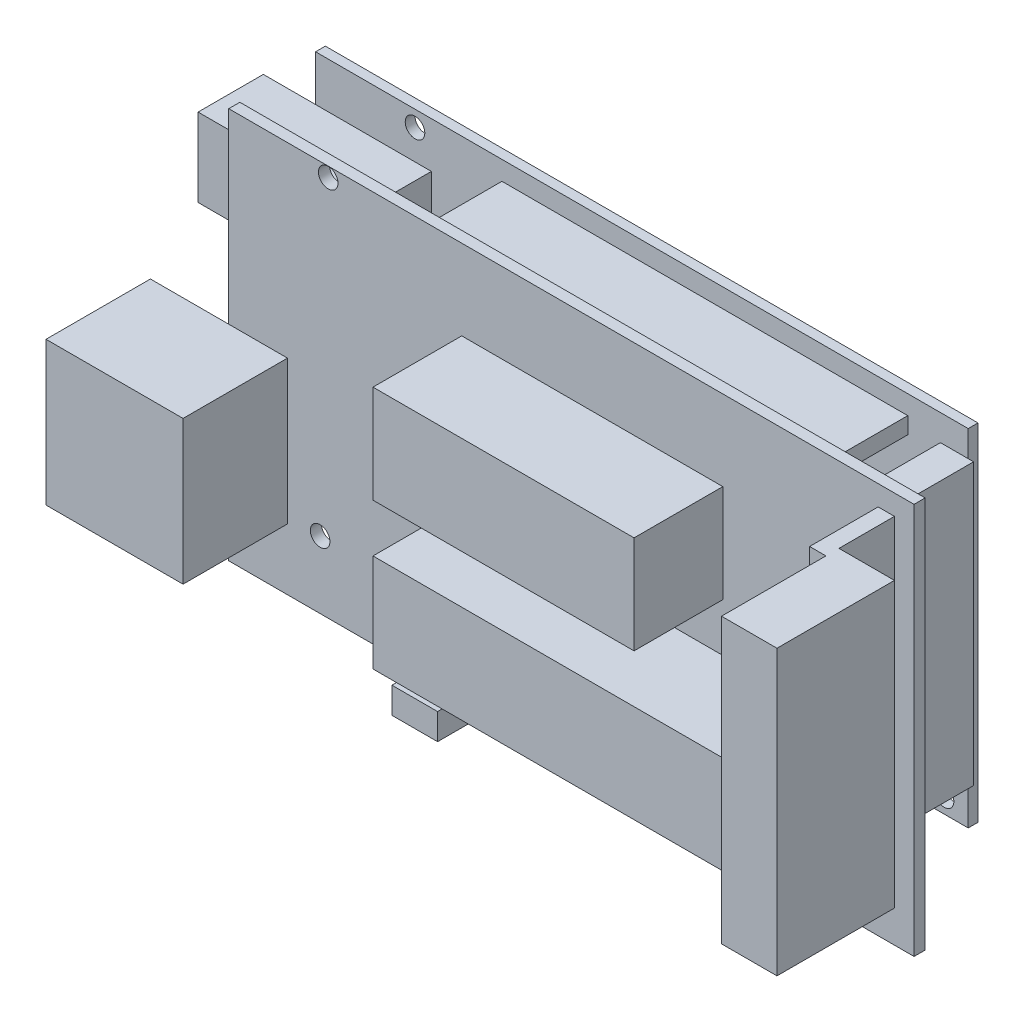
SolidWorks part; units mm, degrees
ref_plane "Plano frontal" through (0, 0, 0) normal (0, 0, 1) x (1, 0, 0)
ref_plane "Plano superior" through (0, 0, 0) normal (0, 1, 0) x (1, 0, 0)
ref_plane "Plano direito" through (0, 0, 0) normal (1, 0, 0) x (0, 0, -1)
sketch "Esboço1" plane through (0, 0, 0) normal (0, 0, 1) x (1, 0, 0)
  line L1 (-52.5, 30) -> (52.5, 30)
  line L2 (-52.5, 30) -> (-52.5, -30)
  line L3 (-52.5, -30) -> (52.5, -30)
  line L4 (52.5, 30) -> (52.5, -30)
  line L5 (-52.5, 30) -> (52.5, -30) construction
  line L6 (-52.5, -30) -> (52.5, 30) construction
  point P0 (0, 0)
  dimension "D1" = 60
  dimension "D2" = 105
extrude "Ressalto-extrusão1" add sketch "Esboço1" along normal blind 1.7
sketch "Esboço2" plane through (0, 0, 1.7) normal (0, 0, 1) x (1, 0, 0)
  line L0 (-52.5, -30) -> (52.5, -30) construction
  line L1 (-16.8, -4.7) -> (43.2, -4.7)
  line L2 (-16.8, -4.7) -> (-16.8, -19.7)
  line L3 (-16.8, -19.7) -> (43.2, -19.7)
  line L4 (43.2, -4.7) -> (43.2, -19.7)
  line L5 (52.5, -30) -> (52.5, 30) construction
  line L7 (-16.8, 2.7) -> (23.2, 2.7)
  line L8 (-16.8, 2.7) -> (-16.8, 17.7)
  line L9 (-16.8, 17.7) -> (23.2, 17.7)
  line L10 (23.2, 2.7) -> (23.2, 17.7)
  dimension "D1" = 60
  dimension "D2" = 15
  dimension "D3" = 10.3
  dimension "D4" = 9.3
  dimension "D5" = 40
  dimension "D6" = 7.4
extrude "Ressalto-extrusão2" add sketch "Esboço2" along normal blind 13.6
sketch "Esboço3" plane through (0, 0, 0) normal (0, 0, -1) x (-1, 0, 0)
  line L0 (52.5, -30) -> (-52.5, -30) construction
  line L1 (52.5, 30.9) -> (-47.5, 30.9)
  line L2 (52.5, 30.9) -> (52.5, -22.1)
  line L3 (52.5, -22.1) -> (-47.5, -22.1)
  line L4 (-47.5, 30.9) -> (-47.5, -22.1)
  line L5 (52.5, 30) -> (52.5, -30) construction
  dimension "D1" = 7.9
  dimension "D2" = 53
  dimension "D3" = 100
extrude "Ressalto-extrusão6" add sketch "Esboço3" along normal blind 1.5 from offset 11.6 separate body
sketch "Esboço4" plane through (0, 0, -11.6) normal (0, 0, 1) x (1, 0, 0)
  line L1 (-23.9415, 27.9898) -> (38.2426, 27.9898)
  line L2 (-23.9415, 27.9898) -> (-23.9415, 25.4498)
  line L3 (-23.9415, 25.4498) -> (38.2426, 25.4498)
  line L4 (38.2426, 27.9898) -> (38.2426, 25.4498)
  line L5 (48.3249, 26.9052) -> (43.2449, 26.9052)
  line L6 (48.3249, 26.9052) -> (48.3249, -16.0526)
  line L7 (48.3249, -16.0526) -> (43.2449, -16.0526)
  line L8 (43.2449, 26.9052) -> (43.2449, -16.0526)
  line L9 (38.2426, -19.9599) -> (-17.8292, -19.9599)
  line L10 (38.2426, -19.9599) -> (38.2426, -17.4199)
  line L11 (38.2426, -17.4199) -> (-17.8292, -17.4199)
  line L12 (-17.8292, -19.9599) -> (-17.8292, -17.4199)
  dimension "D1" = 2.54
  dimension "D2" = 5.08
extrude "Ressalto-extrusão8" add sketch "Esboço4" along normal up to surface (11.6 mm away) up to face at (0, 0, 0)
sketch "Esboço6" plane through (0, 0, 1.7) normal (0, 0, 1) x (1, 0, 0)
  line L1 (-64.5, 1.4) -> (-43.5, 1.4)
  line L2 (-64.5, 1.4) -> (-64.5, -20.6)
  line L3 (-64.5, -20.6) -> (-43.5, -20.6)
  line L4 (-43.5, 1.4) -> (-43.5, -20.6)
  line L5 (-52.5, 30) -> (-52.5, -30) construction
  line L6 (-52.5, 30.9) -> (47.5, 30.9) construction
  dimension "D1" = 22
  dimension "D2" = 29.5
  dimension "D3" = 12
  dimension "D4" = 21
extrude "Ressalto-extrusão9" add sketch "Esboço6" along normal blind 16
sketch "Esboço7" plane through (0, 0, -11.6) normal (0, 0, 1) x (1, 0, 0)
  line L0 (-52.5, 30.9) -> (47.5, 30.9) construction
  line L1 (-34.753, 23.9) -> (-60.5, 23.9)
  line L2 (-34.753, 23.9) -> (-34.753, 11.9)
  line L3 (-34.753, 11.9) -> (-60.5, 11.9)
  line L4 (-60.5, 23.9) -> (-60.5, 11.9)
  line L5 (-52.5, -22.1) -> (-52.5, 30.9) construction
  dimension "D1" = 7
  dimension "D2" = 12
  dimension "D3" = 8
extrude "Ressalto-extrusão10" add sketch "Esboço7" along normal blind 10
sketch "Esboço8" plane through (0, 0, -13.1) normal (0, 0, -1) x (-1, 0, 0)
  line L0 (52.5, -22.1) -> (52.5, 30.9) construction
  line L1 (-47.5, -22.1) -> (52.5, -22.1) construction
  circle A0 centre (37.26, 28.47) radius 1.5
  circle A1 centre (38.5, -19.7) radius 1.5
  circle A2 centre (-43.8, -19.7) radius 1.5
  dimension "D1" = 3
  dimension "D2" = 15.24
  dimension "D3" = 14
  dimension "D4" = 82.3
  dimension "D5" = 2.4
  dimension "D6" = 2.4
  dimension "D7" = 48.17
extrude "Corte-extrusão1" cut sketch "Esboço8" against normal through all
sketch "Esboço9" plane through (0, -30, 0) normal (0, -1, 0) x (1, 0, 0)
  line L0 (49.5, 1.7) -> (49.5, 10.2)
  line L1 (-52.5, 1.7) -> (52.5, 1.7) construction
  line L2 (49.5, 10.2) -> (58, 10.2)
  line L3 (58, 10.2) -> (58, 28.2)
  line L4 (58, 28.2) -> (49.5, 28.2)
  line L5 (49.5, 28.2) -> (49.5, 12.2)
  line L6 (47, 1.7) -> (49.5, 1.7)
  line L7 (49.5, 12.2) -> (47, 12.2)
  line L8 (47, 12.2) -> (47, 1.7)
  line L12 (47.5, -13.1) -> (47.5, -11.6) construction
  dimension "D1" = 8.5
  dimension "D2" = 18
  dimension "D3" = 8.5
  dimension "D4" = 2.5
  dimension "D5" = 0.5
  dimension "D6" = 8.5
  dimension "D7" = 2
extrude "Ressalto-extrusão11" add sketch "Esboço9" against normal up to surface (56.9052 mm away) up to face at (46.1279, 26.9052, -6.96)
sketch "Esboço10" plane through (58, 0, 0) normal (1, 0, 0) x (0, 0, -1)
  line L0 (-10.2, 26.9052) -> (-10.2, -30) construction
  line L1 (-10.2, -16.5737) -> (-28.2, -16.5737)
  line L2 (-10.2, -16.5737) -> (-10.2, 27.4263) construction
  line L3 (-10.2, 27.4263) -> (-28.2, 27.4263) construction
  line L4 (-28.2, -16.5737) -> (-28.2, 27.4263) construction
  line L5 (-10.2, -16.5737) -> (-28.2, 27.4263) construction
  line L6 (-10.2, 27.4263) -> (-28.2, -16.5737) construction
  line L7 (11.6, -16.0526) -> (11.6, 26.9052) construction
  line L8 (-28.2, 26.9052) -> (-28.2, -30) construction
  line L9 (-28.2, -16.5737) -> (-28.2, -30)
  line L10 (-28.2, -30) -> (-1.7, -30)
  line L11 (-10.2, -16.5737) -> (-1.7, -16.5737)
  line L12 (-1.7, -16.5737) -> (-1.7, -30)
  point P0 (-19.2, 5.4263)
  point P10 (11.6, 5.4263)
  dimension "D1" = 44
extrude "Corte-extrusão2" cut sketch "Esboço10" against normal up to surface (11 mm away) up to face at (47, -1.5474, 6.95)
sketch "Esboço12" plane through (0, -30, 0) normal (0, -1, 0) x (1, 0, 0)
  line L0 (-52.5, 1.7) -> (52.5, 1.7) construction
  line L1 (-20.5, 8.7) -> (-13.5, 8.7)
  line L2 (-20.5, 8.7) -> (-20.5, 1.7)
  line L3 (-20.5, 1.7) -> (-13.5, 1.7)
  line L4 (-13.5, 8.7) -> (-13.5, 1.7)
  line L5 (-20.5, 8.7) -> (-13.5, 1.7) construction
  line L6 (-20.5, 1.7) -> (-13.5, 8.7) construction
  line L7 (-52.5, 1.7) -> (-52.5, 0) construction
  point P0 (-17, 5.2)
  point P9 (-52.5, 0.85)
  dimension "D1" = 32
  dimension "D2" = 7
  dimension "D3" = 7
extrude "Ressalto-extrusão12" add sketch "Esboço12" against normal blind 4 from offset 1
equation "\"D5@Esboço2\"=\"D1@Esboço2\"*2/3"
equation "\"D2@Esboço4\"=\"D1@Esboço4\"*2"
